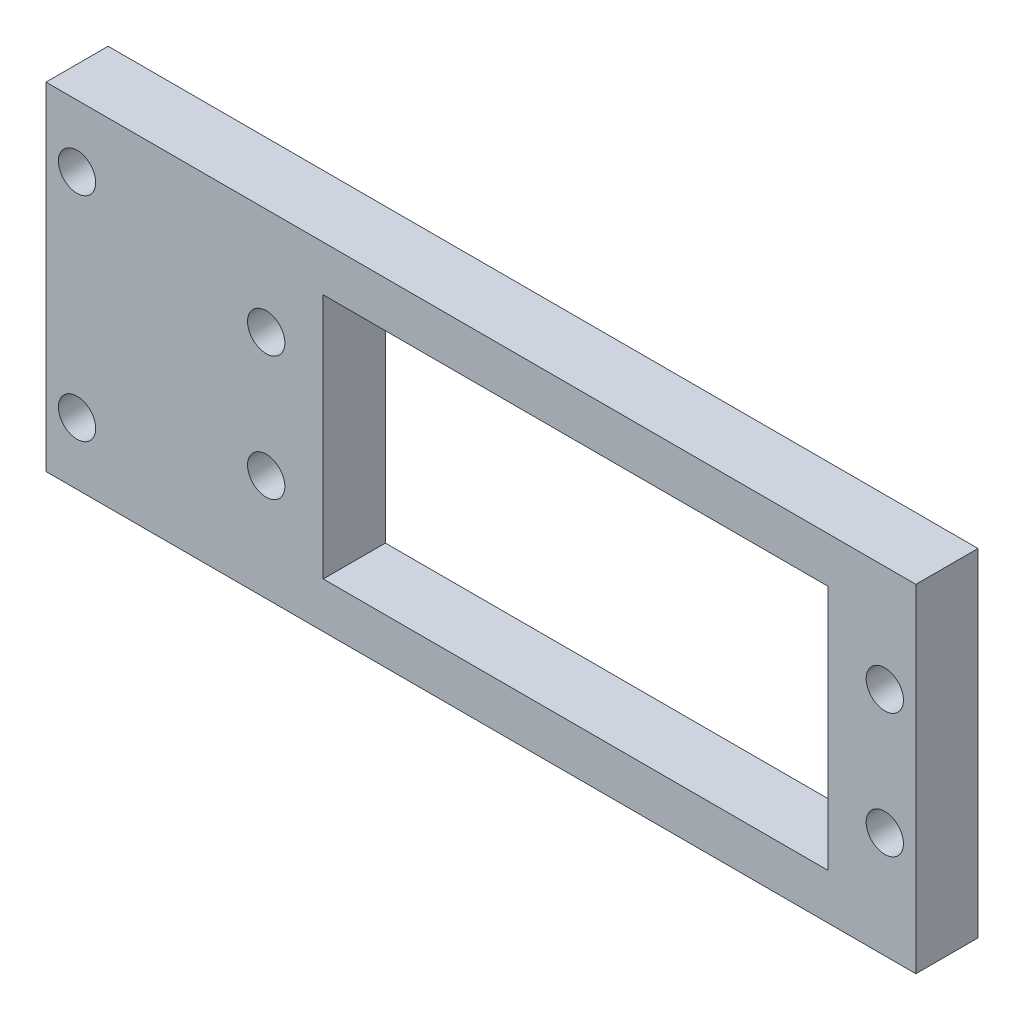
SolidWorks part; units mm, degrees
material "Acrílico (médio-alto impacto)"
ref_plane "Plano frontal" through (0, 0, 0) normal (0, 0, 1) x (1, 0, 0)
ref_plane "Plano superior" through (0, 0, 0) normal (0, 1, 0) x (1, 0, 0)
ref_plane "Plano direito" through (0, 0, 0) normal (1, 0, 0) x (0, 0, -1)
sketch "Esboço1" plane through (0, 0, 0) normal (0, 0, 1) x (1, 0, 0)
  line L1 (-26.7505, 19.6766) -> (43.2495, 19.6766)
  line L2 (-26.7505, 19.6766) -> (-26.7505, -7.4634)
  line L3 (-26.7505, -7.4634) -> (43.2495, -7.4634)
  line L4 (43.2495, 19.6766) -> (43.2495, -7.4634)
  dimension "D1" = 70
  dimension "D2" = 27.14
extrude "Ressalto-extrusão1" add sketch "Esboço1" along normal blind 5
sketch "Esboço2" plane through (0, 0, 5) normal (0, 0, 1) x (1, 0, 0)
  line L0 (-26.7505, -7.4634) -> (43.2495, -7.4634) construction
  line L1 (43.2495, -7.4634) -> (43.2495, 19.6766) construction
  line L2 (43.2495, 19.6766) -> (-26.7505, 19.6766) construction
  line L3 (-26.7505, 19.6766) -> (-26.7505, -7.4634) construction
  line L5 (-26.7505, -7.4634) -> (43.2495, -7.4634) construction
  circle A0 centre (-24.2505, 14.6766) radius 1.5
  circle A1 centre (-24.2505, -2.4634) radius 1.5
  circle A2 centre (40.7495, 11.1066) radius 1.5
  circle A3 centre (40.7495, 1.1066) radius 1.5
  dimension "D2" = 2.5
  dimension "D3" = 2.5
  dimension "D4" = 10
  dimension "D5" = 3
  dimension "D6" = 3
  dimension "D7" = 3
  dimension "D8" = 3
  dimension "D9" = 5
  dimension "D10" = 5
  dimension "D11" = 2.5
  dimension "D12" = 2.5
  dimension "D13" = 8.57
extrude "Corte-extrusão1" cut sketch "Esboço2" against normal blind 5
sketch "Esboço4" plane through (0, 0, 0) normal (0, 0, -1) x (-1, 0, 0)
  line L1 (-36.1595, -3.7934) -> (4.4405, -3.7934)
  line L2 (-36.1595, -3.7934) -> (-36.1595, 16.0066)
  line L3 (-36.1595, 16.0066) -> (4.4405, 16.0066)
  line L4 (4.4405, -3.7934) -> (4.4405, 16.0066)
  line L5 (-43.2495, 19.6766) -> (26.7505, 19.6766) construction
  circle A1 centre (-40.7495, 1.1066) radius 1.5 construction
  dimension "D1" = 4.59
  dimension "D2" = 40.6
  dimension "D3" = 19.8
  dimension "D4" = 3.67
extrude "Corte-extrusão2" cut sketch "Esboço4" against normal through all
sketch "Esboço5" plane through (0, 0, 0) normal (0, 0, -1) x (-1, 0, 0)
  line L0 (26.7505, -7.4634) -> (-43.2495, -7.4634) construction
  line L1 (-43.2495, 19.6766) -> (26.7505, 19.6766) construction
  circle A0 centre (9.0305, 1.1066) radius 1.5
  circle A1 centre (9.0305, 11.1066) radius 1.5
  circle A2 centre (-40.7495, 11.1066) radius 1.5 construction
  circle A3 centre (-40.7495, 1.1066) radius 1.5 construction
  dimension "D1" = 49.78
  dimension "D2" = 49.78
  dimension "D3" = 8.57
  dimension "D4" = 8.57
  dimension "D5" = 3
  dimension "D6" = 3
extrude "Corte-extrusão3" cut sketch "Esboço5" against normal through all
